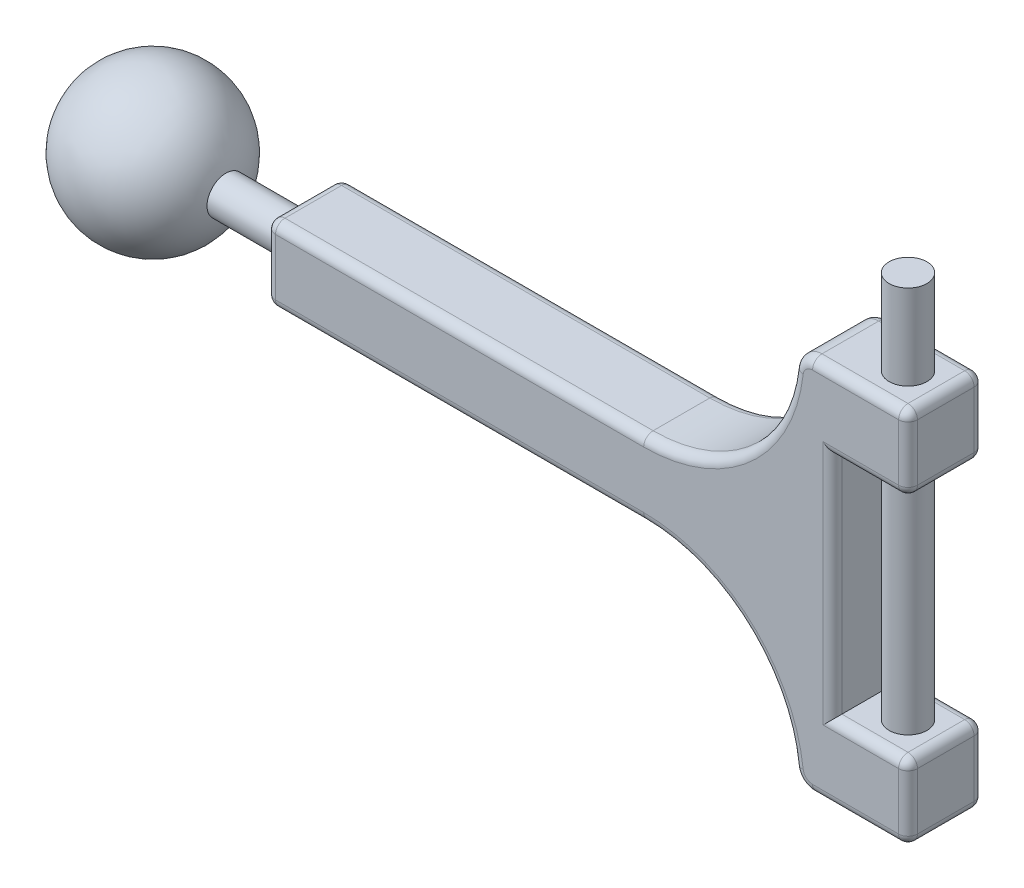
SolidWorks part; units mm, degrees
ref_plane "Front Plane" through (0, 0, 0) normal (0, 0, 1) x (1, 0, 0)
ref_plane "Top Plane" through (0, 0, 0) normal (0, 1, 0) x (1, 0, 0)
ref_plane "Right Plane" through (0, 0, 0) normal (1, 0, 0) x (0, 0, -1)
sketch "Sketch1" plane through (0, 0, 0) normal (0, 0, 1) x (1, 0, 0)
  line L0 (0, 25) -> (0, -25) construction
  line L1 (-100, 0) -> (5, 0) construction
  line L2 (5, 25) -> (5, -25) construction
  line L3 (-5, 25) -> (-5, -25) construction
  line L4 (-80, 5) -> (-30, 5)
  line L5 (-80, -5) -> (-30, -5)
  line L6 (-55, 5) -> (-55, -5) construction
  line L7 (-7.6393, 25) -> (5, 25)
  line L8 (-7.6393, -25) -> (5, -25)
  line L9 (-80, 5) -> (-80, -5)
  line L10 (5, 25) -> (5, 15)
  line L11 (5, 15) -> (-5, 15)
  line L12 (-5, 15) -> (-5, -15)
  line L13 (-5, -15) -> (5, -15)
  line L14 (5, -15) -> (5, -25)
  arc A0 (-30, 5) -> (-10.1238, 22.7778) centre (-30, 25) ccw
  arc A1 (-30, -5) -> (-10.1238, -22.7778) centre (-30, -25) cw
  arc A2 (-7.6393, 25) -> (-10.1238, 22.7778) centre (-7.6393, 22.5) ccw
  arc A3 (-10.1238, -22.7778) -> (-7.6393, -25) centre (-7.6393, -22.5) ccw
  point P8 (-5, 0)
  point P9 (0, 0)
  point P15 (5, 0)
  point P19 (-55, 0)
  point P22 (-55, 5)
  point P24 (-55, -5)
  dimension "D7" = 5
  dimension "D8" = 20
  dimension "D1" = 100
  dimension ".5" = 5
  dimension "D2" = 50
  dimension "D3" = 10
  dimension "D4" = 25
  dimension "D5" = 10
  dimension "D6" = 80
extrude "Boss-Extrude2" add sketch "Sketch1" along normal blind 10
sketch "Sketch2" plane through (-80, 0, 0) normal (-1, 0, 0) x (0, 0, 1)
  line L0 (10, 5) -> (0, -5) construction
  circle A0 centre (5, 0) radius 2.5
  dimension "D1" = 5
extrude "Boss-Extrude3" add sketch "Sketch2" along normal blind 20
sketch "Sketch3" plane through (-100, 0, 0) normal (-1, 0, 0) x (0, 0, 1)
  line L0 (5, 10) -> (5, -10)
  arc A0 (5, 10) -> (5, -10) centre (5, 0) ccw
  dimension "D1" = 20
revolve "Revolve1" add sketch "Sketch3" angle 360 about L0
sketch "Sketch5" plane through (0, 15, 0) normal (0, -1, 0) x (1, 0, 0)
  line L0 (-5, 0) -> (5, 10) construction
  circle A0 centre (0, 5) radius 2.5
  dimension "D1" = 5
extrude "Boss-Extrude4" add sketch "Sketch5" along normal up to surface (30 mm away) up to face at (0, -15, 5)
sketch "Sketch6" plane through (0, 25, 0) normal (0, 1, 0) x (1, 0, 0)
  line L0 (5, 0) -> (-5, -10) construction
  line L1 (5, -10) -> (5, 0) construction
  line L3 (5, -10) -> (-7.6393, -10) construction
  circle A0 centre (0, -5) radius 2.5
  dimension "D2" = 5
  dimension "D1" = 45
extrude "Boss-Extrude5" add sketch "Sketch6" along normal blind 11.25
fillet "Fillet1" radius 1.25 34 edges at (-16.6667, -10.0929, 0) (-9.306, -24.3634, 0) (-1.3197, -25, 0) (0, -15, 0) (-5, 0, 0) (0, 15, 0) (-1.3197, 25, 0) (-9.306, 24.3634, 0) (-16.6667, 10.0929, 0) (-55, -5, 10) (-16.6667, -10.0929, 10) (-9.306, -24.3634, 10) (-1.3197, -25, 10) (-1.3197, 25, 10) (-9.306, 24.3634, 10) (-16.6667, 10.0929, 10) (5, -25, 5) (5, -20, 0) (5, -15, 5) (5, -20, 10) (0, -15, 10) (-5, 0, 10) (0, 15, 10) (5, 15, 5) (5, 25, 5) (5, 20, 10) (5, 20, 0) (-80, -5, 5) (-80, 0, 0) (-80, 5, 5) (-80, 0, 10) (-55, 5, 0) (-55, -5, 0) (-55, 5, 10)
